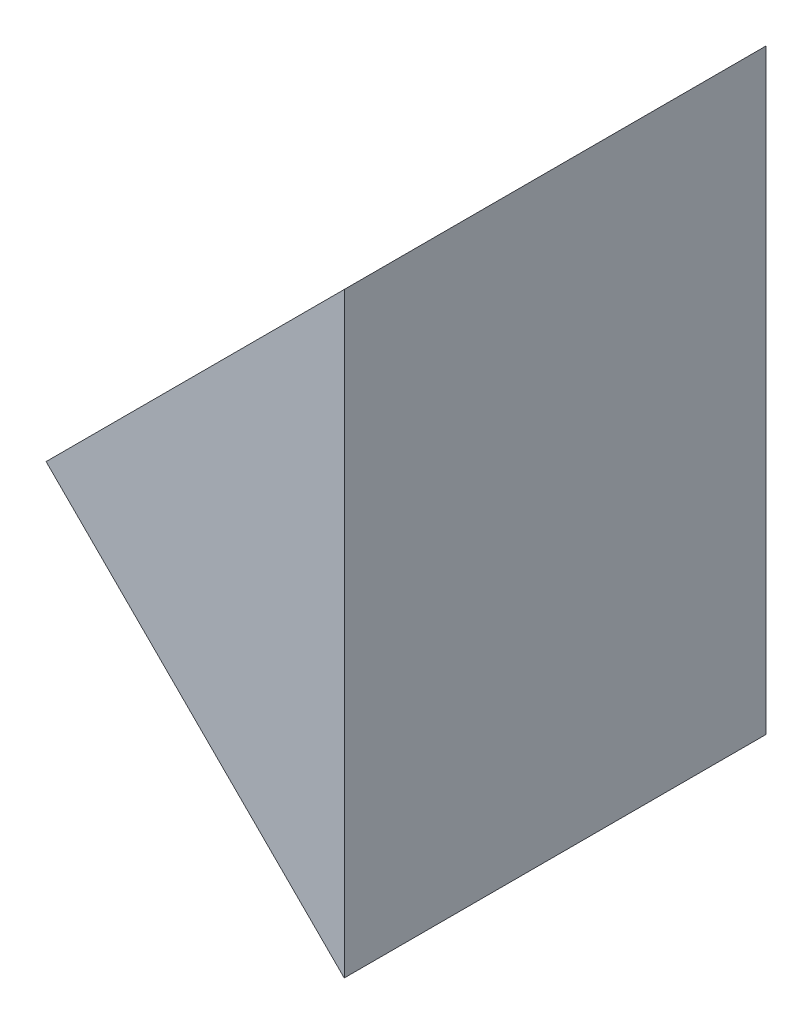
SolidWorks part; units mm, degrees
ref_plane "前视基准面" through (0, 0, 0) normal (0, 0, 1) x (1, 0, 0)
ref_plane "上视基准面" through (0, 0, 0) normal (0, 1, 0) x (1, 0, 0)
ref_plane "右视基准面" through (0, 0, 0) normal (1, 0, 0) x (0, 0, -1)
sketch "草图1" plane through (0, 0, 0) normal (0, 0, 1) x (1, 0, 0)
  line L0 (138.6917, 34.4392) -> (147.5305, 43.2781)
  line L1 (138.6917, 34.4392) -> (147.5305, 25.6004)
  line L2 (147.5305, 25.6004) -> (147.5305, 43.2781)
  dimension "D1" = 12.5
  dimension "D2" = 12.5
extrude "凸台-拉伸1" add sketch "草图1" along normal blind 12.5
